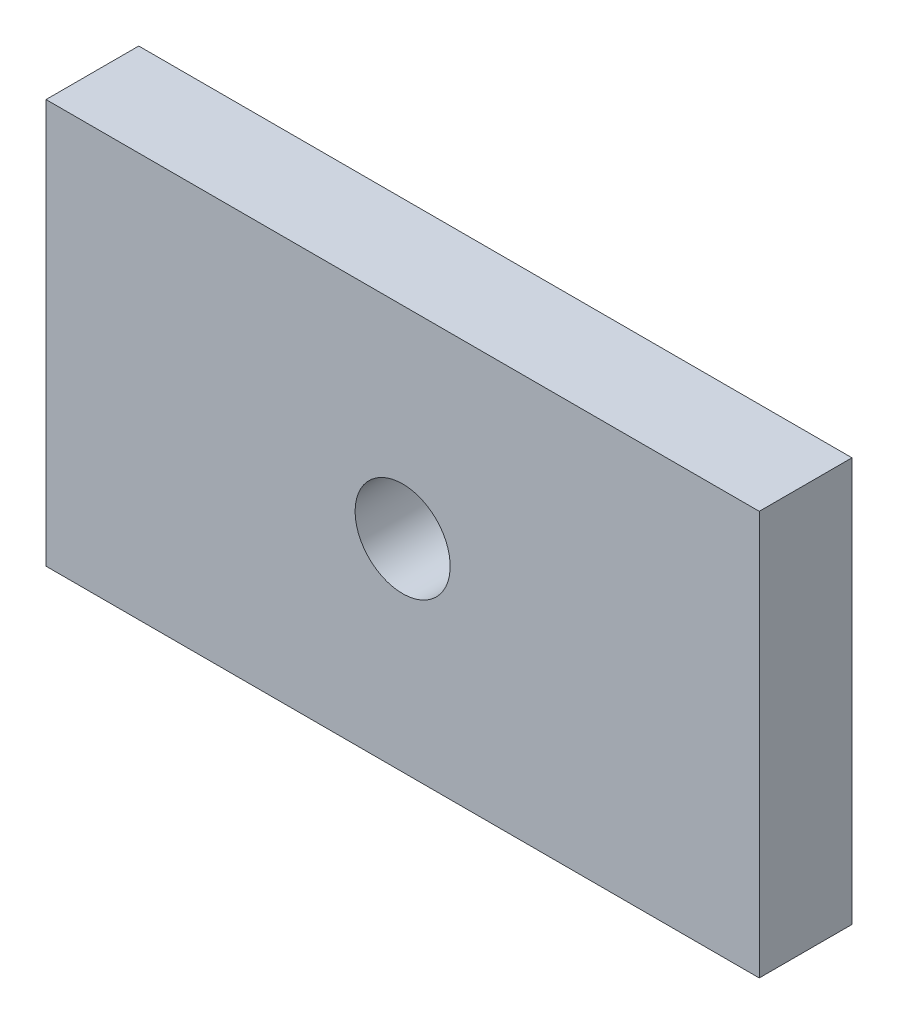
SolidWorks part; units mm, degrees
material "Thornel Mat VMA"
ref_plane "Plan de face" through (0, 0, 0) normal (0, 0, 1) x (1, 0, 0)
ref_plane "Plan de dessus" through (0, 0, 0) normal (0, 1, 0) x (1, 0, 0)
ref_plane "Plan de droite" through (0, 0, 0) normal (1, 0, 0) x (0, 0, -1)
sketch "Esquisse1" plane through (0, 0, 0) normal (0, 0, 1) x (1, 0, 0)
  line L1 (-15, 0) -> (15, 0)
  line L2 (-15, 0) -> (-15, 17)
  line L3 (-15, 17) -> (15, 17)
  line L4 (15, 0) -> (15, 17)
  point P4 (0, 0)
  dimension "D1" = 30
  dimension "D2" = 17
extrude "Boss.-Extru.1" add sketch "Esquisse1" along normal blind 3.9
hole_wizard "Ø4.0 (4) Diameter Hole1" positions "Sketch1" profile "Sketch2" hole size "Ø4.0" standard "ISO" end condition up to next
sketch "Sketch1" plane through (0, 0, 0) normal (0, 0, -1) x (-1, 0, 0)
  line L0 (15, 0) -> (-15, 0) construction
  point P0 (0, 8.5)
  dimension "D1" = 8.5
sketch "Sketch2" plane through (0, 8.5, 0) normal (1, 0, 0) x (0, 1, 0)
  line L0 (0, 0) -> (0, 3.9)
  line L1 (0, 3.9) -> (2, 3.9)
  line L2 (2, 3.9) -> (2, 0)
  line L5 (2, 0) -> (0, 0)
  line L11 (0, -6.35) -> (0, 107.95) construction
  dimension "Thru Hole Dia." = 4
  dimension "Thru Hole Depth" = 3.9
